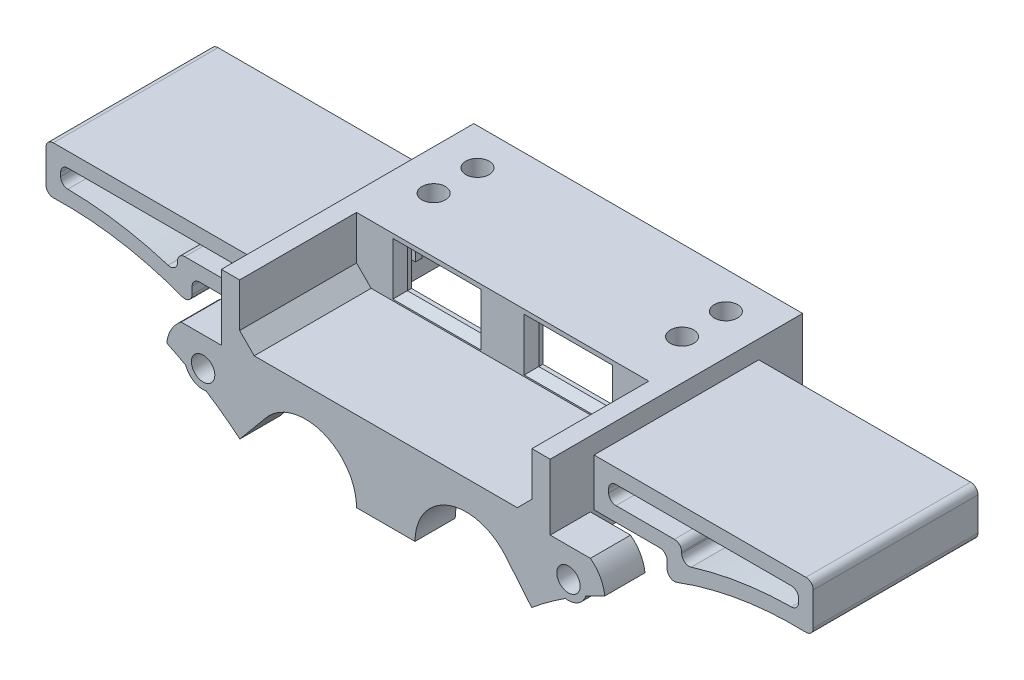
SolidWorks part; units mm, degrees
ref_plane "前视基准面" through (0, 0, 0) normal (0, 0, 1) x (1, 0, 0)
ref_plane "上视基准面" through (0, 0, 0) normal (0, 1, 0) x (1, 0, 0)
ref_plane "右视基准面" through (0, 0, 0) normal (1, 0, 0) x (0, 0, -1)
sketch "草图1" plane through (0, 0, 0) normal (0, 0, 1) x (1, 0, 0)
  line L0 (0, 0) -> (22.5, 0)
  line L1 (22.5, 0) -> (22.5, 12)
  line L2 (22.5, 12) -> (-22.5, 12)
  line L3 (-22.5, 12) -> (-22.5, 0)
  line L4 (-22.5, 0) -> (0, 0)
extrude "凸台-拉伸1" add sketch "草图1" along normal blind 34.55
sketch "草图2" plane through (0, 0, 34.55) normal (0, 0, 1) x (1, 0, 0)
  line L0 (-20, 12) -> (20, 12)
  line L1 (22.5, 12) -> (-22.5, 12) construction
  line L2 (20, 12) -> (20, 4)
  line L3 (20, 4) -> (-20, 4)
  line L4 (0, -6.6) -> (0, 6.6) construction
  line L5 (-20, 12) -> (-20, 4)
  point P9 (0, 4)
  point P10 (0, 12)
extrude "切除-拉伸1" cut sketch "草图2" against normal blind 16
sketch "草图3" plane through (0, 0, 0) normal (0, -1, 0) x (1, 0, 0)
  line L1 (0, 2) -> (20, 2)
  line L2 (20, 2) -> (20, 17)
  line L3 (20, 17) -> (-20, 17)
  line L4 (-20, 17) -> (-20, 2)
  line L5 (-20, 2) -> (0, 2)
extrude "切除-拉伸2" cut sketch "草图3" against normal blind 10
sketch "草图4" plane through (0, 0, 18.55) normal (0, 0, 1) x (1, 0, 0)
  line L0 (-14.04, 10.4) -> (-14.04, 5.2)
  line L1 (-13.94, 10.3) -> (-13.94, 5.3) construction
  line L7 (-13.94, 5.3) -> (-4.04, 5.3) construction
  line L8 (-13.94, 10.3) -> (-4.04, 10.3) construction
  line L9 (-4.04, 10.3) -> (-4.04, 5.3) construction
  line L10 (-14.04, 5.2) -> (-3.94, 5.2)
  line L11 (-3.94, 10.4) -> (-3.94, 5.2)
  line L12 (-14.04, 10.4) -> (-3.94, 10.4)
  line L13 (0, -6.6) -> (0, 6.6) construction
  line L14 (4.04, 10.3) -> (4.04, 5.3) construction
  line L15 (13.94, 10.3) -> (4.04, 10.3) construction
  line L16 (13.94, 5.3) -> (4.04, 5.3) construction
  line L17 (13.94, 10.3) -> (13.94, 5.3) construction
  line L18 (14.04, 10.4) -> (3.94, 10.4)
  line L19 (3.94, 10.4) -> (3.94, 5.2)
  line L20 (14.04, 5.2) -> (3.94, 5.2)
  line L21 (14.04, 10.4) -> (14.04, 5.2)
  dimension "D1" = 0.1
extrude "切除-拉伸3" cut sketch "草图4" against normal blind 10
chamfer "倒角1" distance 2 angle 45 2 edges at (20, 4, 26.55) (-20, 4, 26.55)
chamfer "倒角2" distance 1 angle 45 8 edges at (-8.99, 5.2, 18.55) (-14.04, 7.8, 18.55) (-8.99, 10.4, 18.55) (-3.94, 7.8, 18.55) (8.99, 10.4, 18.55) (3.94, 7.8, 18.55) (8.99, 5.2, 18.55) (14.04, 7.8, 18.55)
sketch "草图6" plane through (0, 12, 0) normal (0, 1, 0) x (1, 0, 0)
  line L0 (22.5, 0) -> (22.5, -13.5)
  line L2 (22.5, -34.55) -> (22.5, 0) construction
  line L3 (22.5, -13.5) -> (17, -13.5)
  line L4 (14.5, -11) -> (14.5, -5)
  line L5 (14.5, -5) -> (14.5, 0)
  line L6 (22.5, 0) -> (-22.5, 0) construction
  line L7 (14.5, 0) -> (22.5, 0)
  line L8 (0, -6.6) -> (0, 6.6) construction
  line L9 (-14.5, 0) -> (-22.5, 0)
  line L10 (-14.5, -5) -> (-14.5, 0)
  line L11 (-14.5, -11) -> (-14.5, -5)
  line L12 (-22.5, -13.5) -> (-17, -13.5)
  line L13 (-22.5, 0) -> (-22.5, -13.5)
  circle A0 centre (17, -5) radius 1.6
  circle A1 centre (17, -11) radius 1.6
  arc A2 (17, -13.5) -> (14.5, -11) centre (17, -11) cw
  arc A3 (-17, -13.5) -> (-14.5, -11) centre (-17, -11) ccw
  circle A4 centre (-17, -11) radius 1.6
  circle A5 centre (-17, -5) radius 1.6
extrude "凸台-拉伸2" add sketch "草图6" against normal blind 6.9
sketch "草图7" plane through (0, 12, 0) normal (0, 1, 0) x (1, 0, 0)
  circle A0 centre (17, -5) radius 1.6
  circle A1 centre (17, -11) radius 1.6
  circle A2 centre (-17, -5) radius 1.6
  circle A3 centre (-17, -11) radius 1.6
extrude "切除-拉伸4" cut sketch "草图7" against normal blind 10
sketch "草图8" plane through (0, 0, 34.55) normal (0, 0, 1) x (1, 0, 0)
  line L1 (1.843, -25.3671) -> (9.2306, -19.6151)
  line L2 (-18, 4) -> (18, 4) construction
  line L3 (0, -6.6) -> (0, 6.6) construction
  line L5 (16.5232, -2.6996) -> (19.968, -6.8465)
  line L6 (-1.843, -25.3671) -> (-9.2306, -19.6151)
  line L7 (-5.4768, -11.3004) -> (-10.4216, -17.6514)
  line L8 (5.4768, -11.3004) -> (10.4216, -17.6514)
  line L9 (-16.5232, -2.6996) -> (-19.968, -6.8465)
  line L10 (22.5, 3) -> (22.5, 4)
  line L11 (-22.5, 12) -> (-22.5, 0) construction
  line L12 (-22.5, 3) -> (-28, 3)
  line L13 (-22.5, 3) -> (-22.5, 4)
  line L14 (22.5, 3) -> (28, 3)
  line L15 (-22.5, 4) -> (22.5, 4)
  circle A1 centre (25, -1) radius 1.6
  circle A3 centre (0, -23) radius 1.6
  arc A4 (-1.843, -25.3671) -> (1.843, -25.3671) centre (0, -23) ccw
  circle A6 centre (-25, -1) radius 1.6
  arc A8 (29.9729, -0.4804) -> (27.3654, -1.8093) centre (50, -43) ccw
  arc A9 (10.4216, -17.6514) -> (9.2306, -19.6151) centre (50, -43) ccw
  arc A10 (16.5232, -2.6996) -> (5.4768, -11.3004) centre (11, -7) ccw
  arc A11 (24.5837, -3.4651) -> (27.3654, -1.8093) centre (25, -1) ccw
  arc A12 (24.5837, -3.4651) -> (19.968, -6.8465) centre (50, -43) ccw
  arc A13 (-10.4216, -17.6514) -> (-9.2306, -19.6151) centre (-50, -43) cw
  arc A14 (-16.5232, -2.6996) -> (-5.4768, -11.3004) centre (-11, -7) cw
  arc A15 (-24.5837, -3.4651) -> (-19.968, -6.8465) centre (-50, -43) cw
  arc A16 (-24.5837, -3.4651) -> (-27.3654, -1.8093) centre (-25, -1) cw
  arc A17 (-29.9729, -0.4804) -> (-27.3654, -1.8093) centre (-50, -43) cw
  arc A18 (-29.9729, -0.4804) -> (-28, 3) centre (-25, -1) cw
  arc A19 (29.9729, -0.4804) -> (28, 3) centre (25, -1) ccw
  point P23 (0, 4)
extrude "凸台-拉伸3" add sketch "草图8" against normal blind 5.5
sketch "草图10" plane through (0, 0, 0) normal (0, 0, -1) x (-1, 0, 0)
  line L1 (22.5, 0) -> (-22.5, 0) construction
  line L2 (-20, 0) -> (-20, 10)
  line L3 (-20, 10) -> (20, 10)
  line L4 (20, 10) -> (20, 0)
  line L5 (20, 0) -> (-20, 0)
extrude "切除-拉伸5" cut sketch "草图10" against normal blind 2
sketch "草图11" plane through (0, 0, 29.05) normal (0, 0, -1) x (-1, 0, 0)
  line L0 (-4, -7) -> (4, -7)
  line L1 (-4, -7) -> (-10.4216, -17.6514)
  line L2 (-10.4216, -17.6514) -> (-10.4216, -27.0892)
  line L3 (-10.4216, -27.0892) -> (10.4216, -27.0892)
  line L4 (0, 19.0025) -> (0, -19.0025) construction
  line L5 (10.4216, -17.6514) -> (10.4216, -27.0892)
  line L6 (4, -7) -> (10.4216, -17.6514)
  arc A0 (-5.4768, -11.3004) -> (-11, 0) centre (-11, -7) ccw construction
  arc A1 (11, 0) -> (5.4768, -11.3004) centre (11, -7) ccw construction
  point P16 (0, -27.0892)
extrude "切除-拉伸6" cut sketch "草图11" against normal blind 10
sketch "草图12" plane through (0, 5.1, 0) normal (0, -1, 0) x (1, 0, 0)
  line L1 (17, 11) -> (17, 13.5)
  line L2 (17, 13.5) -> (-17, 13.5)
  line L3 (-17, 13.5) -> (-17, 11)
  line L4 (-17, 11) -> (17, 11)
extrude "切除-拉伸7" cut sketch "草图12" against normal up to surface (4.9 mm away) up to face at (0, 10, 10.0562)
sketch "草图14" plane through (0, 0, 0) normal (0, 0, -1) x (-1, 0, 0)
  line L0 (-22.5, 9.5) -> (-52.5, 9.5)
  line L1 (-52.5, 9.5) -> (-52.5, 2.932)
  line L2 (-22.5, 9.5) -> (-22.5, 3)
  line L3 (-22.5, 3) -> (-32.5, 3)
  line L4 (-32.5, 3) -> (-32.5, -0.4588)
  line L5 (0, 10.45) -> (0, -10.45) construction
  line L6 (32.5, 3) -> (32.5, -0.4588)
  line L7 (22.5, 3) -> (32.5, 3)
  line L8 (22.5, 9.5) -> (22.5, 3)
  line L9 (52.5, 9.5) -> (52.5, 2.932)
  line L10 (22.5, 9.5) -> (52.5, 9.5)
  line L11 (-24.5, 7.5) -> (-50.5, 7.5)
  line L12 (-50.5, 7.5) -> (-50.5, 4.9974)
  line L13 (-34.5, 5) -> (-34.5, 2.4285)
  line L14 (-24.5, 5) -> (-34.5, 5)
  line L15 (-24.5, 7.5) -> (-24.5, 5)
  line L16 (34.5, 5) -> (34.5, 2.4285)
  line L17 (50.5, 7.5) -> (50.5, 4.9974)
  line L18 (24.5, 7.5) -> (50.5, 7.5)
  line L19 (24.5, 7.5) -> (24.5, 5)
  line L20 (24.5, 5) -> (34.5, 5)
  arc A0 (-32.5, -0.4588) -> (-52.5, 2.932) centre (-50, -43) ccw
  arc A1 (32.5, -0.4588) -> (52.5, 2.932) centre (50, -43) cw
  arc A2 (-34.5, 2.4285) -> (-50.5, 4.9974) centre (-50, -43) ccw
  arc A3 (34.5, 2.4285) -> (50.5, 4.9974) centre (50, -43) cw
  dimension "D1" = 2
extrude "凸台-拉伸4" add sketch "草图14" against normal blind 22.55 from offset 6 offset against normal yes
fillet "圆角1" radius 1 20 edges at (32.5, 3, 17.275) (-32.5, -0.4588, 17.275) (-52.5, 2.932, 17.275) (32.5, -0.4588, 17.275) (52.5, 2.932, 17.275) (52.5, 9.5, 17.275) (-32.5, 3, 17.275) (-34.5, 2.4285, 17.275) (-34.5, 5, 17.275) (-24.5, 7.5, 17.275) (-24.5, 5, 17.275) (-50.5, 7.5, 17.275) (-50.5, 4.9974, 17.275) (34.5, 2.4285, 17.275) (34.5, 5, 17.275) (24.5, 5, 17.275) (24.5, 7.5, 17.275) (50.5, 7.5, 17.275) (50.5, 4.9974, 17.275) (-52.5, 9.5, 17.275)
